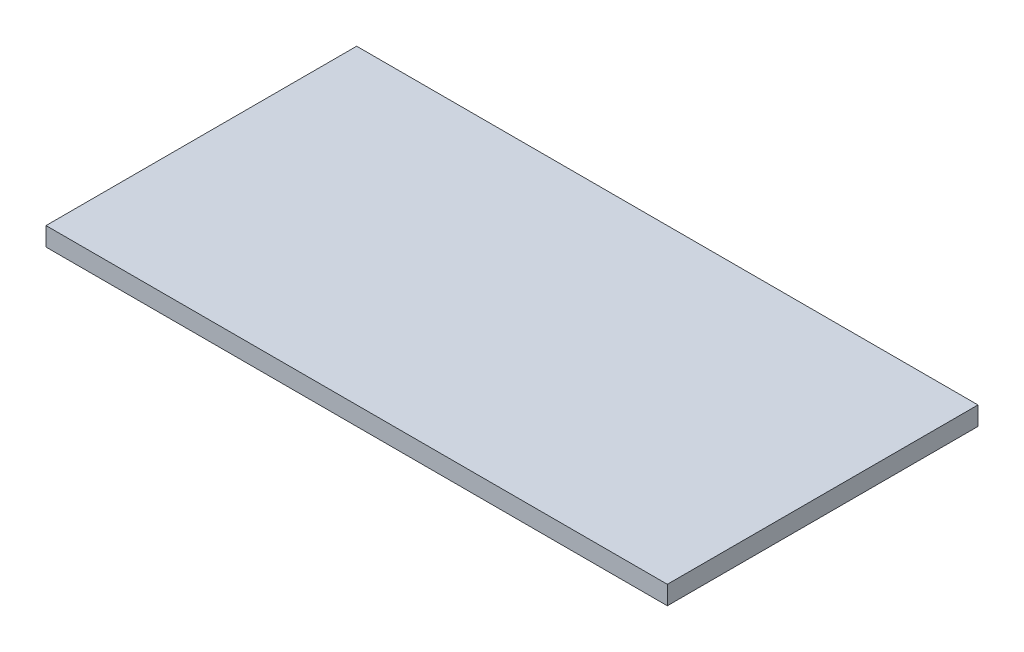
SolidWorks part; units mm, degrees
ref_plane "Спереди" through (0, 0, 0) normal (0, 0, 1) x (1, 0, 0)
ref_plane "Сверху" through (0, 0, 0) normal (0, 1, 0) x (1, 0, 0)
ref_plane "Справа" through (0, 0, 0) normal (1, 0, 0) x (0, 0, -1)
sketch "Эскиз1" plane through (0, 0, 0) normal (0, 1, 0) x (1, 0, 0)
  line L1 (0, 0) -> (600, 0)
  line L2 (0, 0) -> (0, 300)
  line L3 (0, 300) -> (600, 300)
  line L4 (600, 0) -> (600, 300)
  dimension "D1" = 600
  dimension "D2" = 300
extrude "Бобышка-Вытянуть1" add sketch "Эскиз1" along normal blind 18
